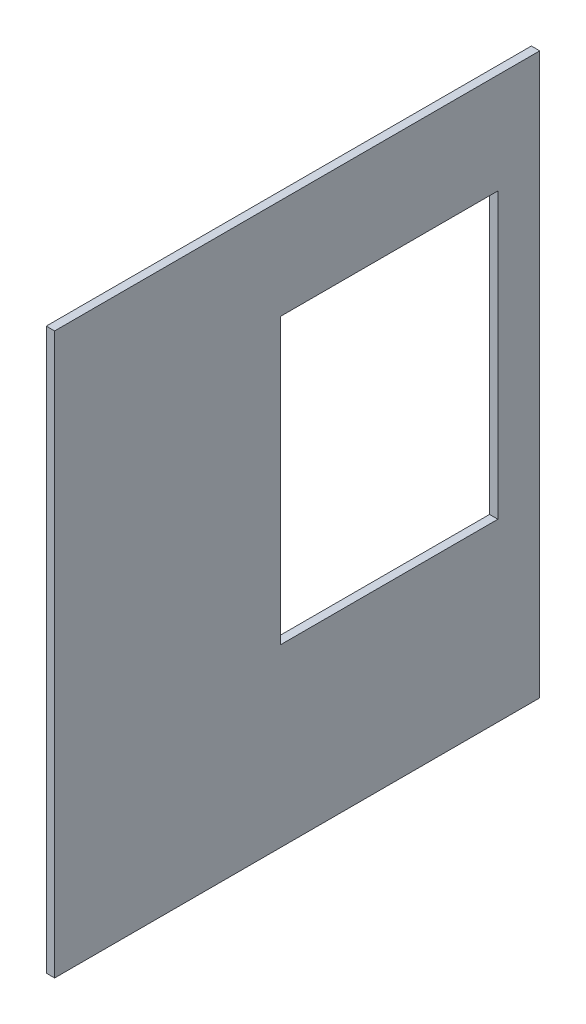
SolidWorks part; units mm, degrees
ref_plane "Plan de face" through (0, 0, 0) normal (0, 0, 1) x (1, 0, 0)
ref_plane "Plan de dessus" through (0, 0, 0) normal (0, 1, 0) x (1, 0, 0)
ref_plane "Plan de droite" through (0, 0, 0) normal (1, 0, 0) x (0, 0, -1)
sketch "Esquisse1" plane through (0, 0, 0) normal (1, 0, 0) x (0, 0, -1)
  line L1 (-64.591, 39.7217) -> (515.409, 39.7217)
  line L2 (-64.591, 39.7217) -> (-64.591, -630.2783)
  line L3 (-64.591, -630.2783) -> (515.409, -630.2783)
  line L4 (515.409, 39.7217) -> (515.409, -630.2783)
  line L5 (465.409, -80.2783) -> (205.409, -80.2783)
  line L6 (465.409, -80.2783) -> (465.409, -420.2783)
  line L7 (465.409, -420.2783) -> (205.409, -420.2783)
  line L8 (205.409, -80.2783) -> (205.409, -420.2783)
  dimension "D1" = 580
  dimension "D2" = 670
  dimension "D3" = 270
  dimension "D4" = 340
  dimension "D5" = 210
  dimension "D6" = 260
extrude "Boss.-Extru.1" add sketch "Esquisse1" along normal blind 10
equation "\"ProfondeurPlacard\"=580"
equation "\"D1@Esquisse1\"=\"ProfondeurPlacard\""
equation "\"EpaisseurPlaque\"= 10"
equation "\"LargeurPlacard\"=160+70+135"
equation "\"DistanceAvantSyphon\"=240"
equation "\"DistanceAvantEvier\"=100"
equation "\"DiametreTuyau\"=90"
equation "\"HauteurTuyau\"=430"
equation "\"LargeurAeration\"=260"
equation "\"HauteurAeration\"=340"
equation "\"AerationSol\"=210"
equation "\"AerationAvant\"=270"
equation "\"ProfondeurCharniere\"=80"
equation "\"HauteurCharniere\"=60"
equation "\"LargeurCharniere\"=60"
equation "\"HauteurPlacard\"=650"
equation "\"HauteurEvier\"=\"HauteurPlacard\"-555"
equation "\"HauteurDroitEvier\"=\"HauteurPlacard\" -500"
equation "\"HauteurSolSyphon\"=320"
equation "\"DiametreSyphon\"=70"
equation "\"PositionSyphonCoteGauche\"=160"
equation "\"D2@Esquisse1\"=\"HauteurPlacard\"+2*\"EpaisseurPlaque\""
equation "\"D3@Esquisse1\"=\"AerationAvant\""
equation "\"D4@Esquisse1\"=\"HauteurAeration\""
equation "\"D5@Esquisse1\"=\"AerationSol\""
equation "\"D6@Esquisse1\"=\"LargeurAeration\""
